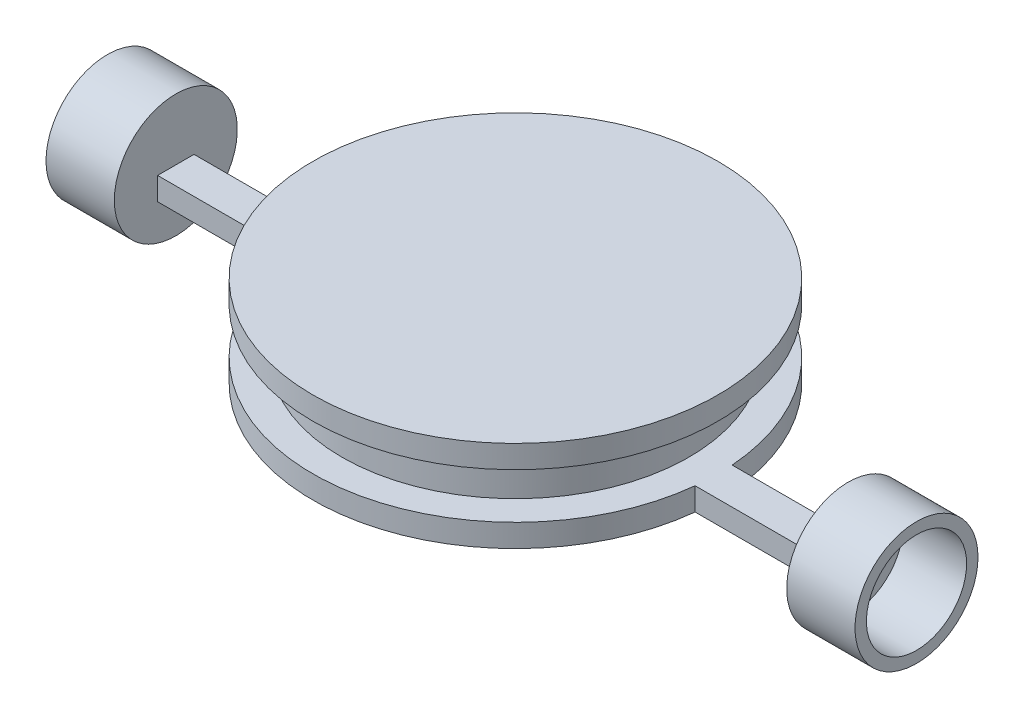
SolidWorks part; units mm, degrees
ref_plane "Front Plane" through (0, 0, 0) normal (0, 0, 1) x (1, 0, 0)
ref_plane "Top Plane" through (0, 0, 0) normal (0, 1, 0) x (1, 0, 0)
ref_plane "Right Plane" through (0, 0, 0) normal (1, 0, 0) x (0, 0, -1)
sketch "Sketch1" plane through (0, 0, 0) normal (0, 1, 0) x (1, 0, 0)
  circle A0 centre (0, 0) radius 44.45
  dimension "D1" = 88.9
extrude "Boss-Extrude1" add sketch "Sketch1" along normal blind 5
sketch "Sketch2" plane through (0, 5, 0) normal (0, 1, 0) x (1, 0, 0)
  circle A0 centre (0, 0) radius 38.1
extrude "Boss-Extrude2" add sketch "Sketch2" along normal blind 10
sketch "Sketch3" plane through (0, 15, 0) normal (0, 1, 0) x (1, 0, 0)
  circle A0 centre (0, 0) radius 44.45
extrude "Boss-Extrude3" add sketch "Sketch3" along normal blind 5
sketch "Sketch4" plane through (0, 0, 0) normal (0, 1, 0) x (1, 0, 0)
  line L0 (-44.3311, 3.2487) -> (-73.8054, 3.2487)
  line L1 (-73.8054, 3.2487) -> (-73.8054, -4.7513)
  line L2 (-73.8054, -4.7513) -> (-44.1953, -4.7513)
  line L3 (0, 0) -> (0, -22.9986) construction
  line L4 (73.8054, -4.7513) -> (44.1953, -4.7513)
  line L5 (44.3311, 3.2487) -> (73.8054, 3.2487)
  line L6 (73.8054, 3.2487) -> (73.8054, -4.7513)
  circle A0 centre (0, 0) radius 44.45
  dimension "D1" = 8
extrude "Boss-Extrude4" add sketch "Sketch4" along normal blind 5 contours A0 L0 L1 L2 | A0 L4 L6 L5
sketch "Sketch5" plane through (-73.8054, 0, 0) normal (-1, 0, 0) x (0, 0, 1)
  line L0 (-3.2487, 5) -> (4.7513, 5) construction
  circle A0 centre (0.7513, 5) radius 13.5
  dimension "D1" = 27
extrude "Boss-Extrude5" add sketch "Sketch5" along normal blind 15 contours A0
sketch "Sketch6" plane through (73.8054, 0, 0) normal (1, 0, 0) x (0, 0, -1)
  line L0 (3.2487, 5) -> (-4.7513, 5) construction
  circle A0 centre (-0.7513, 5) radius 13.5
  dimension "D1" = 27
extrude "Boss-Extrude6" add sketch "Sketch6" along normal blind 15
sketch "Sketch7" plane through (88.8054, 0, 0) normal (1, 0, 0) x (0, 0, -1)
  circle A0 centre (-0.7513, 5) radius 11
extrude "Cut-Extrude1" cut sketch "Sketch7" against normal blind 14
sketch "Sketch8" plane through (-88.8054, 0, 0) normal (-1, 0, 0) x (0, 0, 1)
  circle A0 centre (0.7513, 5) radius 11
extrude "Cut-Extrude2" cut sketch "Sketch8" against normal blind 14
